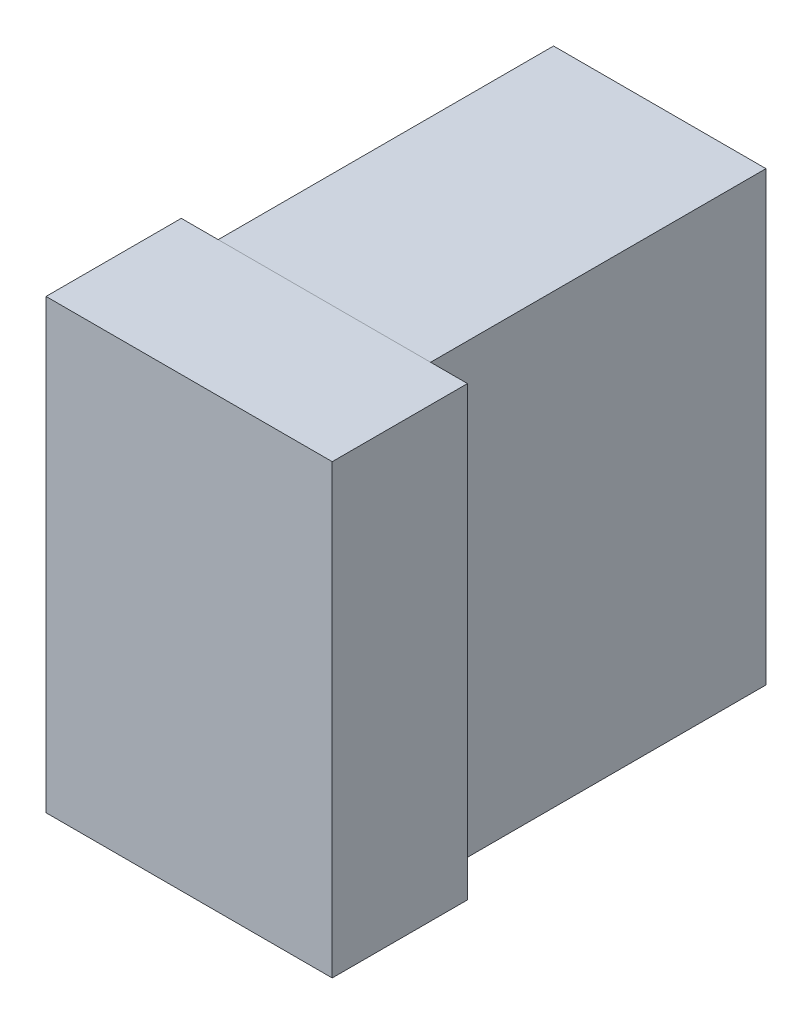
SolidWorks part; units mm, degrees
ref_plane "前视基准面" through (0, 0, 0) normal (0, 0, 1) x (1, 0, 0)
ref_plane "上视基准面" through (0, 0, 0) normal (0, 1, 0) x (1, 0, 0)
ref_plane "右视基准面" through (0, 0, 0) normal (1, 0, 0) x (0, 0, -1)
sketch "草图1" plane through (0, 0, 0) normal (0, 1, 0) x (1, 0, 0)
  line L0 (0, -58.12) -> (0, 66.7303) construction
  line L1 (-69.9195, 0) -> (81.4531, 0) construction
  line L2 (-6.4, 6.05) -> (-6.4, 0)
  line L3 (-6.4, 0) -> (6.4, 0)
  line L4 (6.4, 0) -> (6.4, 6.05)
  line L5 (6.4, 6.05) -> (-6.4, 6.05)
  dimension "D1" = 12.8
  dimension "D2" = 6.05
extrude "凸台-拉伸1" add sketch "草图1" along normal blind 20
sketch "草图2" plane through (0, 0, 0) normal (0, -1, 0) x (1, 0, 0)
  line L0 (4.75, -6.05) -> (-4.75, -6.05)
  line L1 (6.4, -6.05) -> (-6.4, -6.05) construction
  line L2 (-4.75, -6.05) -> (-4.75, -21.05)
  line L3 (-4.75, -21.05) -> (4.75, -21.05)
  line L4 (4.75, -21.05) -> (4.75, -6.05)
  line L5 (0, -18.5779) -> (0, 20.4868) construction
  point P9 (-4.75, -13.55)
  dimension "D1" = 9.5
  dimension "D2" = 15
extrude "凸台-拉伸2" add sketch "草图2" against normal up to surface (20 mm away) separate body up to face at (0, 20, -3.025)
